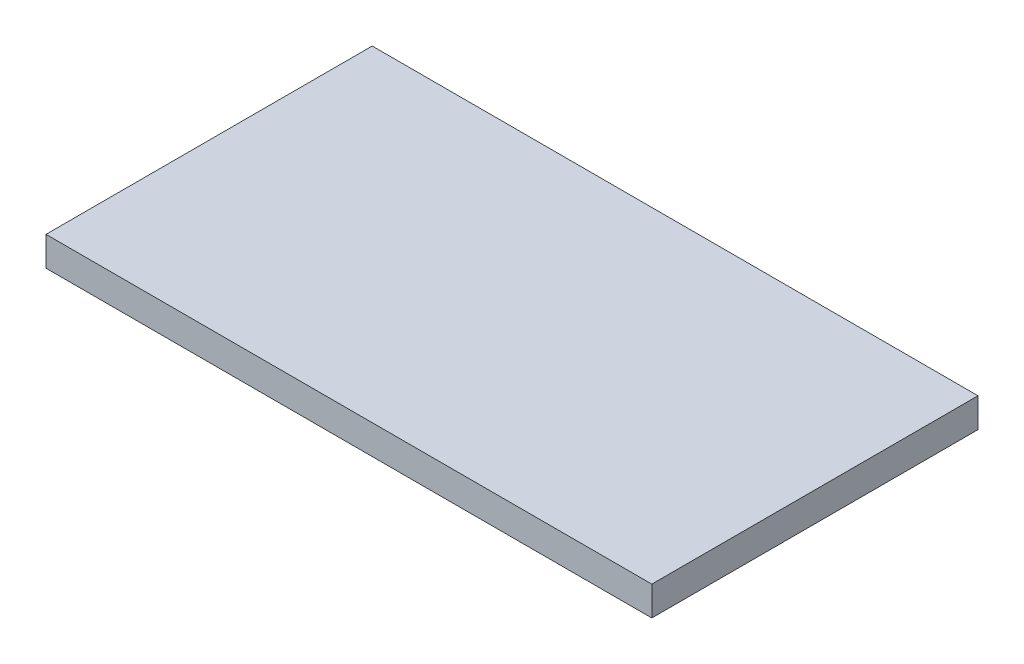
SolidWorks part; units mm, degrees
material "E-Glass Fiber"
ref_plane "Front Plane" through (0, 0, 0) normal (0, 0, 1) x (1, 0, 0)
ref_plane "Top Plane" through (0, 0, 0) normal (0, 1, 0) x (1, 0, 0)
ref_plane "Right Plane" through (0, 0, 0) normal (1, 0, 0) x (0, 0, -1)
sketch "Sketch1" plane through (0, 0, 0) normal (0, 1, 0) x (1, 0, 0)
  line L0 (0, 7.62) -> (-3.81, 7.62) construction
  line L1 (-3.81, 16.51) -> (29.21, 16.51)
  line L2 (-3.81, 16.51) -> (-3.81, -1.27)
  line L3 (-3.81, -1.27) -> (29.21, -1.27)
  line L4 (29.21, 16.51) -> (29.21, -1.27)
  line L5 (0, 0) -> (27.94, 0) construction
  line L6 (0, 0) -> (0, 15.24) construction
  line L7 (0, 15.24) -> (27.94, 15.24) construction
  line L8 (27.94, 0) -> (27.94, 15.24) construction
  line L10 (27.94, 7.62) -> (29.21, 7.62) construction
  dimension "D1" = 33.02
  dimension "D2" = 17.78
  dimension "D3" = 15.24
  dimension "D4" = 27.94
  dimension "D5" = 1.27
extrude "Boss-Extrude2" add sketch "Sketch1" along normal blind 1.6
sketch "Sketch2" plane through (0, 0, 0) normal (0, 1, 0) x (1, 0, 0)
  line L0 (0, -0.88) -> (0, 0.88) construction
  line L2 (-0.88, 0) -> (0.88, 0) construction
  circle A0 centre (0, 0) radius 0.45
  circle A1 centre (0, 15.24) radius 0.45
  dimension "D1" = 0.9
  dimension "D2" = 15.24
extrude "Cut-Extrude2" [suppressed] cut sketch "Sketch2" along normal blind 1.6
pattern_linear "LPattern3" [suppressed] count 12 spacing 2.54
ref_plane "Plane3" through (0, 0, -5.08) normal (0, 0, 1) x (1, 0, 0)
sketch "Sketch9" plane through (0, 0, 0) normal (0, 1, 0) x (1, 0, 0)
  line L0 (-0.88, 0) -> (0.88, 0) construction
  line L2 (-3.81, 16.51) -> (-3.81, -1.27) construction
  circle A0 centre (-0.06, 5.725) radius 0.4
  circle A1 centre (-0.06, 9.475) radius 0.4
  dimension "D1" = 0.8
  dimension "D2" = 3.75
  dimension "D3" = 5.725
  dimension "D4" = 3.75
extrude "Cut-Extrude6" [suppressed] cut sketch "Sketch9" along normal blind 10
